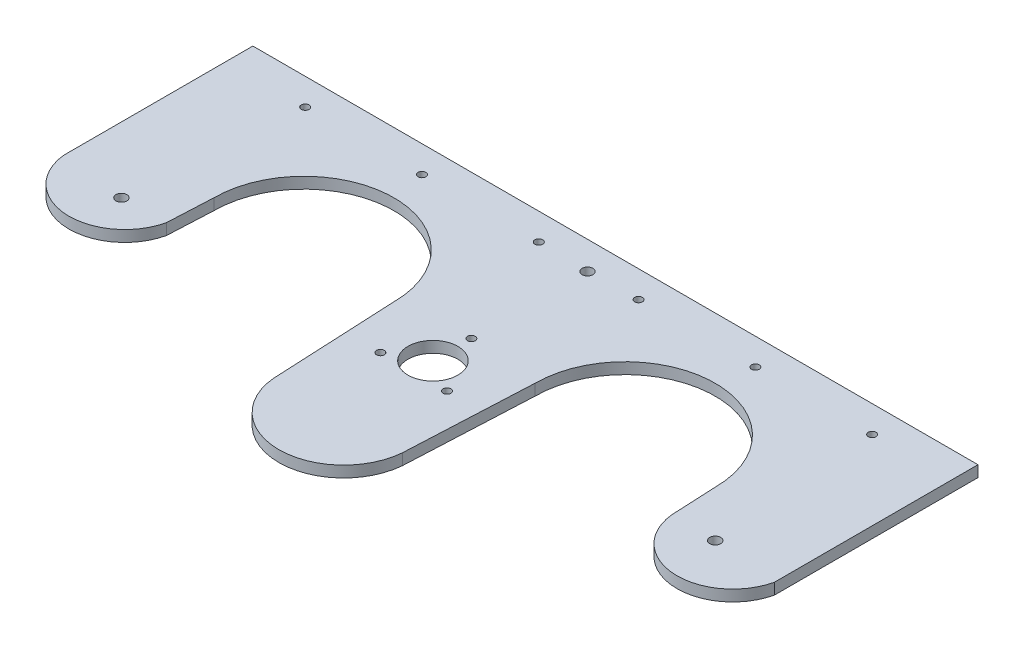
SolidWorks part; units mm, degrees
ref_plane "Plan de face" through (0, 0, 0) normal (0, 0, 1) x (1, 0, 0)
ref_plane "Plan de dessus" through (0, 0, 0) normal (0, 1, 0) x (1, 0, 0)
ref_plane "Plan de droite" through (0, 0, 0) normal (1, 0, 0) x (0, 0, -1)
sketch "Esquisse2" plane through (0, 0, 0) normal (0, 1, 0) x (1, 0, 0)
  line L1 (0, 0) -> (298, 0)
  line L2 (0, 0) -> (0, 145)
  line L3 (0, 145) -> (298, 145)
  line L4 (298, 0) -> (298, 145)
  dimension "D1" = 145
  dimension "D2" = 298
extrude "Boss.-Extru.1" add sketch "Esquisse2" along normal blind 4.6
sketch "Esquisse3" plane through (0, 4.6, 0) normal (0, 1, 0) x (1, 0, 0)
  line L0 (0, 145) -> (0, 120) construction
  line L1 (0, 145) -> (0, 0) construction
  line L2 (0, 120) -> (298, 120) construction
  line L3 (298, 0) -> (298, 145) construction
  line L4 (149, 145) -> (149, 0) construction
  line L5 (0, 0) -> (298, 0) construction
  line L6 (75, 120) -> (75, 0) construction
  line L7 (225, 120) -> (225, 0) construction
  line L8 (0, 83) -> (298, 83) construction
  line L9 (46, 83) -> (42, 0)
  line L14 (120, 83) -> (124, 0)
  line L15 (124, 0) -> (42, 0)
  line L20 (298, 145) -> (0, 145) construction
  line L21 (174, 0) -> (256, 0)
  line L22 (252, 83) -> (256, 0)
  line L23 (178, 83) -> (174, 0)
  arc A2 (46, 83) -> (120, 83) centre (83, 83) cw
  arc A4 (252, 83) -> (178, 83) centre (215, 83) ccw
  point P24 (42, 0)
  point P29 (124, 0)
  dimension "D4" = 37
  dimension "D1" = 25
  dimension "D2" = 66
  dimension "D3" = 82
  dimension "D5" = 25
extrude "creux_stockage_verre" cut sketch "Esquisse3" against normal blind 46.6
sketch "Esquisse6" plane through (0, 4.6, 0) normal (0, 1, 0) x (1, 0, 0)
  line L0 (149, 145) -> (149, 0) construction
  line L1 (298, 145) -> (0, 145) construction
  line L2 (124, 0) -> (174, 0) construction
  circle A0 centre (149, 70) radius 10.25
  point P1 (149, 70)
  dimension "D2" = 20.5
  dimension "D1" = 70
extrude "trou_bille" cut sketch "Esquisse6" against normal through all
sketch "Esquisse7" plane through (0, 4.6, 0) normal (0, 1, 0) x (1, 0, 0)
  line L0 (0, 145) -> (0, 0) construction
  line L1 (298, 145) -> (0, 145) construction
  line L2 (149, 145) -> (149, 0) construction
  line L3 (124, 0) -> (174, 0) construction
  circle A0 centre (32.5, 134) radius 1.6
  circle A1 centre (80.5, 134) radius 1.6
  circle A2 centre (128.5, 134) radius 1.6
  circle A3 centre (217.5, 134) radius 1.6
  circle A4 centre (169.5, 134) radius 1.6
  circle A5 centre (265.5, 134) radius 1.6
  point P0 (32.5, 134)
  dimension "D3" = 3.2
  dimension "D1" = 32.5
  dimension "D2" = 11
  dimension "D4" = 3
extrude "Enlèv. mat.-Extru.3" cut sketch "Esquisse7" against normal through all
sketch "Esquisse9" plane through (0, 4.6, 0) normal (0, 1, 0) x (1, 0, 0)
  line L0 (124, 0) -> (120, 83) construction
  line L1 (178, 83) -> (174, 0) construction
  line L2 (123.1011, 18.6515) -> (120.0586, -9.9421)
  line L3 (120.0586, -9.9421) -> (178.7898, -9.9421)
  line L4 (178.7898, -9.9421) -> (174.8989, 18.6515)
  arc A0 (123.1011, 18.6515) -> (174.8989, 18.6515) centre (149, 70) ccw
extrude "Enlèv. mat.-Extru.7" cut sketch "Esquisse9" against normal blind 29
sketch "Esquisse12" plane through (0, 4.6, 0) normal (0, 1, 0) x (1, 0, 0)
  line L0 (0, 0) -> (42, 0) construction
  line L1 (17, 0) -> (37, 0) construction
  line L2 (17, 0) -> (17, 54) construction
  line L3 (17, 54) -> (37, 54) construction
  line L4 (37, 0) -> (37, 54) construction
  line L5 (0, 145) -> (0, 0) construction
  line L6 (17, 54) -> (37, 54) construction
  line L7 (17, 54) -> (17, 74) construction
  line L8 (17, 74) -> (37, 74) construction
  line L9 (37, 54) -> (37, 74) construction
  dimension "D1" = 54
  dimension "D2" = 20
  dimension "D3" = 20
  dimension "D4" = 17
sketch "Esquisse13" plane through (0, 4.6, 0) normal (0, 1, 0) x (1, 0, 0)
  line L0 (17, 54) -> (17, 74) construction
  line L2 (17, 74) -> (37, 74) construction
  line L3 (149, 70) -> (149, -20.9546) construction
  line L4 (149, -20.9546) -> (149, 168.1651) construction
  circle A0 centre (27, 64) radius 2.25
  circle A1 centre (271, 64) radius 2.25
  circle A2 centre (149, 133.5194) radius 2.25
  dimension "D3" = 4.5
  dimension "D4" = 4.5
  dimension "D1" = 10
  dimension "D2" = 10
sketch "Esquisse14" plane through (0, 4.6, 0) normal (0, 1, 0) x (1, 0, 0)
  line L0 (46, 83) -> (42, 0) construction
  line L1 (0, 145) -> (0, 0) construction
  line L2 (0, 71.7078) -> (298, 71.7078) construction
  line L3 (298, 0) -> (298, 145) construction
  line L4 (45.1014, 64.3544) -> (252.8986, 64.3544) construction
  line L5 (256, 0) -> (252, 83) construction
  line L6 (0, 71.7078) -> (-22.1588, -9.529)
  line L7 (-22.1588, -9.529) -> (50.381, -9.529)
  line L8 (50.381, -9.529) -> (45.1014, 64.3544)
  line L12 (252.8986, 64.3544) -> (243.7072, -12.3737)
  line L13 (243.7072, -12.3737) -> (332.1502, -12.3737)
  line L14 (332.1502, -12.3737) -> (298, 71.7078)
  line L15 (80.5086, 31) -> (206.1294, 31) construction
  line L16 (298, 145) -> (0, 145) construction
  arc A0 (45.1014, 64.3544) -> (0, 71.7078) centre (22.7978, 69.5466) cw
  arc A3 (298, 71.7078) -> (252.8986, 64.3544) centre (275.6964, 66.5157) cw
  dimension "D1" = 22.9
  dimension "D2" = 22.9
  dimension "D3" = 114
extrude "Enlèv. mat.-Extru.9" cut sketch "Esquisse13" against normal blind 35
sketch "Esquisse15" plane through (0, 4.6, 0) normal (0, 1, 0) x (1, 0, 0)
  line L0 (178, 83) -> (174.8989, 18.6515) construction
  line L1 (123.1011, 18.6515) -> (120, 83) construction
  line L3 (298, 145) -> (0, 145) construction
  arc A0 (175.494, 31) -> (122.506, 31) centre (149, 32.5386) cw
  arc A1 (175.494, 31) -> (122.506, 31) centre (149, 95.7936) cw
  point P11 (149, 6)
  point P18 (122.506, 31)
  dimension "D1" = 139
sketch "Esquisse17" plane through (0, 4.6, 0) normal (0, 1, 0) x (1, 0, 0)
  line L1 (149, 85.81) -> (135.3081, 62.095) construction
  line L2 (135.3081, 62.095) -> (162.6919, 62.095) construction
  line L3 (162.6919, 62.095) -> (149, 85.81) construction
  circle A0 centre (149, 70) radius 7.905 construction
  circle A1 centre (149, 85.81) radius 1.6
  circle A2 centre (135.3081, 62.095) radius 1.6
  circle A3 centre (162.6919, 62.095) radius 1.6
  dimension "D2" = 3.2
  dimension "D3" = 3.2
  dimension "D4" = 3.2
  dimension "D1" = 15.81
extrude "Enlèv. mat.-Extru.14" cut sketch "Esquisse17" against normal blind 4.6
extrude "Boss.-Extru.5" add sketch "Esquisse15" against normal blind 4.6
sketch "Esquisse18" plane through (0, 4.6, 0) normal (0, 1, 0) x (1, 0, 0)
  line L0 (80.5086, 31) -> (206.1294, 31) construction
  line L1 (123.1011, 18.6515) -> (120, 83) construction
  line L2 (178, 83) -> (174.8989, 18.6515) construction
  line L3 (175.494, 31) -> (178.8476, -7.0098)
  line L4 (178.8476, -7.0098) -> (115.9732, -7.0098)
  line L5 (115.9732, -7.0098) -> (122.506, 31)
  arc A0 (122.506, 31) -> (175.494, 31) centre (149, 33.2867) ccw
extrude "Enlèv. mat.-Extru.15" cut sketch "Esquisse18" against normal blind 4.6
extrude "Enlèv. mat.-Extru.16" cut sketch "Esquisse14" against normal blind 4.6
